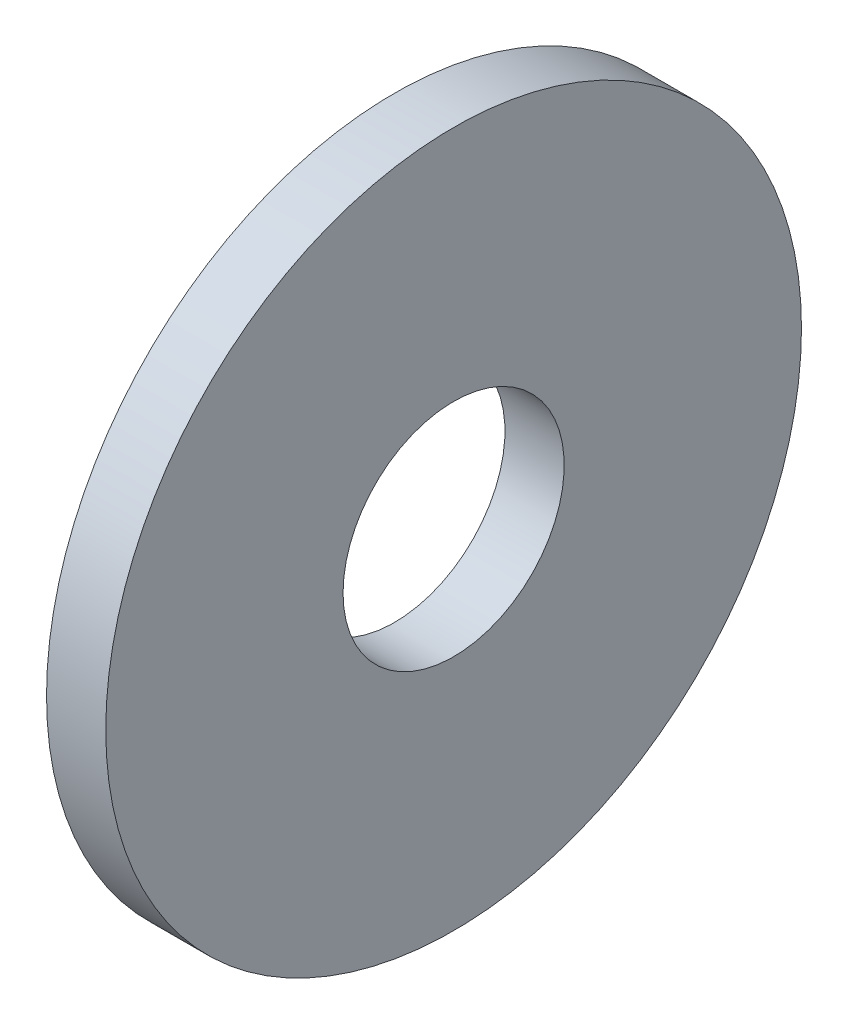
SolidWorks part; units mm, degrees
material "Alumina"
ref_plane "Front Plane" through (0, 0, 0) normal (0, 0, 1) x (1, 0, 0)
ref_plane "Top Plane" through (0, 0, 0) normal (0, 1, 0) x (1, 0, 0)
ref_plane "Right Plane" through (0, 0, 0) normal (1, 0, 0) x (0, 0, -1)
sketch "Sketch1" plane through (0, 0, 0) normal (0, 0, 1) x (1, 0, 0)
  line L0 (-16.7627, -2.0938) -> (34.5053, -2.0938) construction
  line L1 (-16.7627, -2.5938) -> (-16.7627, -1.5938) construction
  line L2 (34.5053, -5.0938) -> (34.5053, 0.9062) construction
  line L4 (13.4089, 3.5062) -> (10.4089, 3.5062)
  line L5 (13.4089, 3.5062) -> (13.4089, 15.5236)
  line L6 (13.4089, 15.5236) -> (10.4089, 15.5236)
  line L7 (10.4089, 3.5062) -> (10.4089, 15.5236)
  line L8 (13.4089, 15.5236) -> (13.4089, -19.7112) construction
  line L10 (36.2373, 3.4062) -> (13.4089, 3.4062) construction
  dimension "D1" = 3
  dimension "D2" = 0.1
revolve "Revolve1" add sketch "Sketch1" angle 360 about L0
